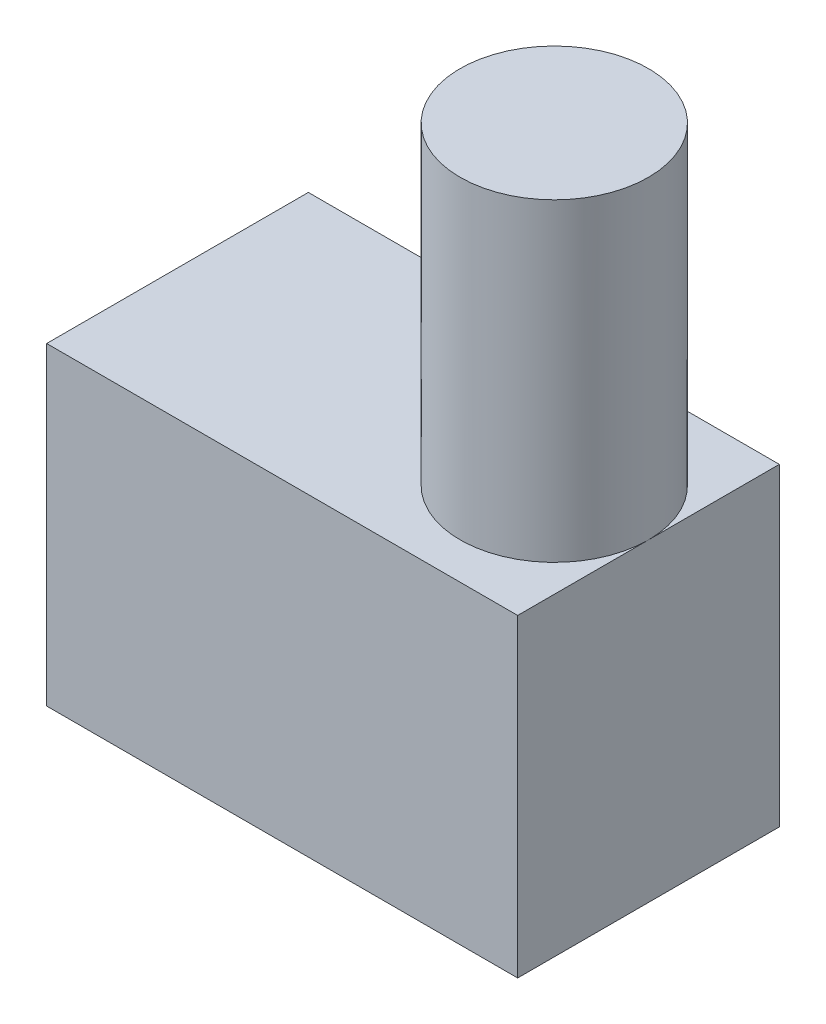
SolidWorks part; units mm, degrees
ref_plane "Front" through (0, 0, 0) normal (0, 0, 1) x (1, 0, 0)
ref_plane "Top" through (0, 0, 0) normal (0, 1, 0) x (1, 0, 0)
ref_plane "Right" through (0, 0, 0) normal (1, 0, 0) x (0, 0, -1)
sketch "Sketch1" plane through (0, 0, 0) normal (0, 0, 1) x (1, 0, 0)
  line L1 (-22.5, 15) -> (22.5, 15)
  line L2 (-22.5, 15) -> (-22.5, -15)
  line L3 (-22.5, -15) -> (22.5, -15)
  line L4 (22.5, 15) -> (22.5, -15)
  line L5 (-22.5, 15) -> (22.5, -15) construction
  line L6 (-22.5, -15) -> (22.5, 15) construction
  point P0 (0, 0)
  dimension "D1" = 45
  dimension "D2" = 30
extrude "Boss-Extrude1" add sketch "Sketch1" along normal blind 25
sketch "Sketch2" plane through (0, 15, 0) normal (0, 1, 0) x (1, 0, 0)
  line L0 (22.5, -25) -> (22.5, 0) construction
  line L3 (-22.5, 0) -> (22.5, -25) construction
  circle A0 centre (13.5, -12.5) radius 9
  point P4 (0, -12.5)
  dimension "D1" = 18
extrude "Boss-Extrude2" add sketch "Sketch2" along normal blind 30
